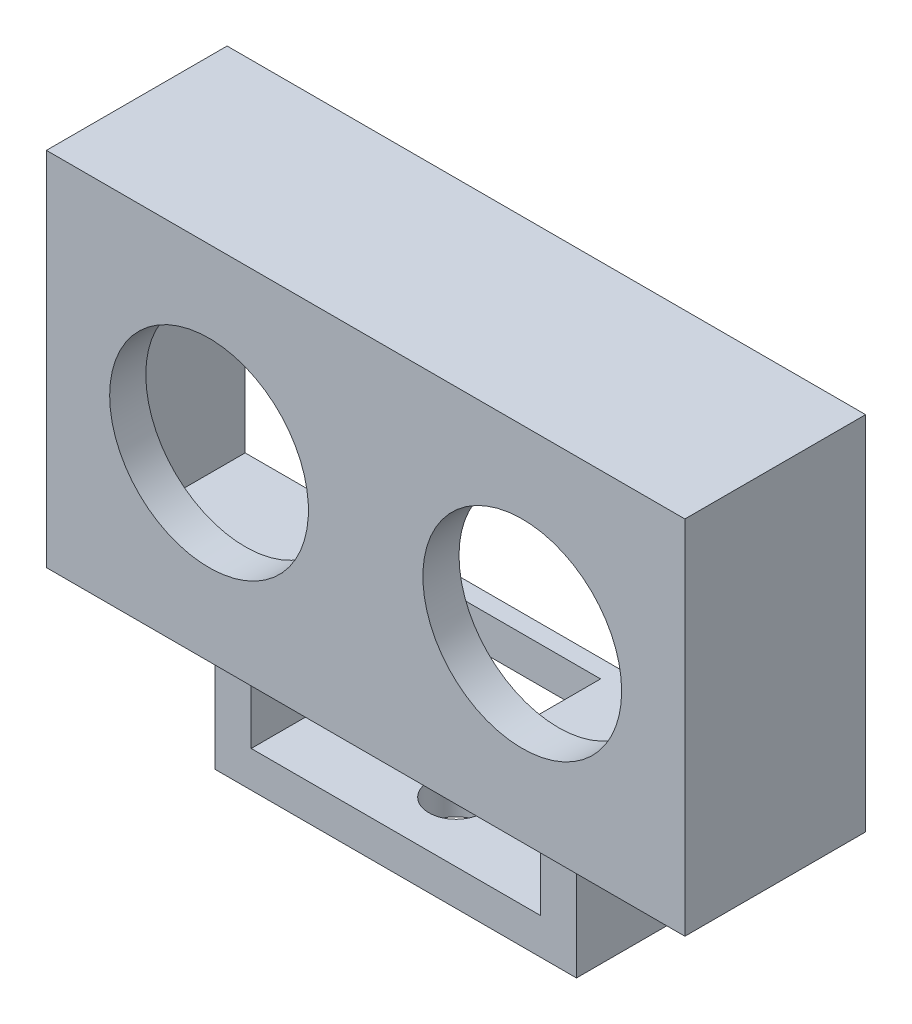
SolidWorks part; units mm, degrees
ref_plane "Front Plane" through (0, 0, 0) normal (0, 0, 1) x (1, 0, 0)
ref_plane "Top Plane" through (0, 0, 0) normal (0, 1, 0) x (1, 0, 0)
ref_plane "Right Plane" through (0, 0, 0) normal (1, 0, 0) x (0, 0, -1)
sketch "Sketch1" plane through (0, 0, 0) normal (0, 0, 1) x (1, 0, 0)
  line L1 (-26.5, 15) -> (26.5, 15)
  line L2 (-26.5, 15) -> (-26.5, -15)
  line L3 (-26.5, -15) -> (26.5, -15)
  line L4 (26.5, 15) -> (26.5, -15)
  line L5 (-26.5, 15) -> (26.5, -15) construction
  line L6 (-26.5, -15) -> (26.5, 15) construction
  point P0 (0, 0)
  dimension "D1" = 53
  dimension "D2" = 30
extrude "Boss-Extrude1" add sketch "Sketch1" along normal blind 15
sketch "Sketch2" plane through (0, 0, 15) normal (0, 0, 1) x (1, 0, 0)
  line L0 (26.5, -15) -> (26.5, 15) construction
  line L1 (0, -13.1699) -> (0, 14.4678) construction
  circle A0 centre (13, 0) radius 8.25
  circle A1 centre (-13, 0) radius 8.25
  dimension "D1" = 16.5
  dimension "D2" = 13.5
extrude "Cut-Extrude1" cut sketch "Sketch2" against normal through all
sketch "Sketch3" plane through (0, 0, 0) normal (0, 0, -1) x (-1, 0, 0)
  line L0 (-26.5, 15) -> (26.5, 15) construction
  line L1 (-23.5, 12) -> (23.5, 12)
  line L2 (-23.5, 12) -> (-23.5, -12)
  line L3 (-23.5, -12) -> (23.5, -12)
  line L4 (23.5, 12) -> (23.5, -12)
  line L5 (-23.5, 12) -> (23.5, -12) construction
  line L6 (-23.5, -12) -> (23.5, 12) construction
  line L7 (26.5, 15) -> (26.5, -15) construction
  point P0 (0, 0)
  dimension "D1" = 3
  dimension "D2" = 3
extrude "Cut-Extrude2" cut sketch "Sketch3" against normal blind 12
sketch "Sketch4" plane through (0, -12, 0) normal (0, 1, 0) x (1, 0, 0)
  line L0 (26.5, 0) -> (-26.5, 0) construction
  line L1 (-7.5, -3) -> (7.5, -3)
  line L2 (-7.5, -3) -> (-7.5, -9)
  line L3 (-7.5, -9) -> (7.5, -9)
  line L4 (7.5, -3) -> (7.5, -9)
  line L5 (-7.5, -3) -> (7.5, -9) construction
  line L6 (-7.5, -9) -> (7.5, -3) construction
  point P0 (0, -6)
  dimension "D1" = 6
  dimension "D2" = 15
  dimension "D3" = 3
extrude "Cut-Extrude3" cut sketch "Sketch4" against normal blind 12
sketch "Sketch6" plane through (0, 0, 0) normal (0, 0, -1) x (-1, 0, 0)
  line L0 (-26.5, 15) -> (26.5, 15) construction
  line L1 (-25, 13.5) -> (25, 13.5)
  line L2 (-25, 13.5) -> (-25, -13.5)
  line L3 (-25, -13.5) -> (25, -13.5)
  line L4 (25, 13.5) -> (25, -13.5)
  line L5 (-25, 13.5) -> (25, -13.5) construction
  line L6 (-25, -13.5) -> (25, 13.5) construction
  line L7 (-26.5, -15) -> (-26.5, 15) construction
  point P0 (0, 0)
  dimension "D1" = 1.5
  dimension "D2" = 1.5
extrude "Cut-Extrude4" cut sketch "Sketch6" against normal blind 1.5
sketch "Sketch7" plane through (0, -15, 0) normal (0, -1, 0) x (1, 0, 0)
  line L1 (-26.5, 15) -> (-26.5, 0) construction
  line L2 (-15, 12.5) -> (15, 12.5)
  line L3 (-15, 12.5) -> (-15, 2.5)
  line L4 (-15, 2.5) -> (15, 2.5)
  line L5 (15, 12.5) -> (15, 2.5)
  line L6 (-15, 12.5) -> (15, 2.5) construction
  line L7 (-15, 2.5) -> (15, 12.5) construction
  point P0 (0, 7.5)
  point P5 (-15, 7.5)
  point P8 (-26.5, 7.5)
  dimension "D1" = 10
  dimension "D2" = 30
extrude "Boss-Extrude2" add sketch "Sketch7" along normal blind 10
sketch "Sketch8" plane through (0, 0, 12.5) normal (0, 0, 1) x (1, 0, 0)
  line L0 (-26.5, -15) -> (26.5, -15) construction
  line L5 (-12, -15) -> (12, -15)
  line L6 (-12, -15) -> (-12, -22)
  line L7 (-12, -22) -> (12, -22)
  line L8 (12, -15) -> (12, -22)
  line L9 (-12, -15) -> (12, -22) construction
  line L10 (-12, -22) -> (12, -15) construction
  line L11 (-15, -25) -> (-15, -15) construction
  line L13 (15, -25) -> (-15, -25) construction
  point P0 (0, -18.5)
  dimension "D1" = 3
  dimension "D2" = 3
extrude "Cut-Extrude5" cut sketch "Sketch8" against normal through all
sketch "Sketch9" plane through (0, -25, 0) normal (0, -1, 0) x (1, 0, 0)
  line L0 (15, 2.5) -> (15, 12.5) construction
  circle A0 centre (0, 7.5) radius 2.25
  point P5 (15, 7.5)
  dimension "D1" = 4.5
extrude "Cut-Extrude6" cut sketch "Sketch9" against normal blind 4
